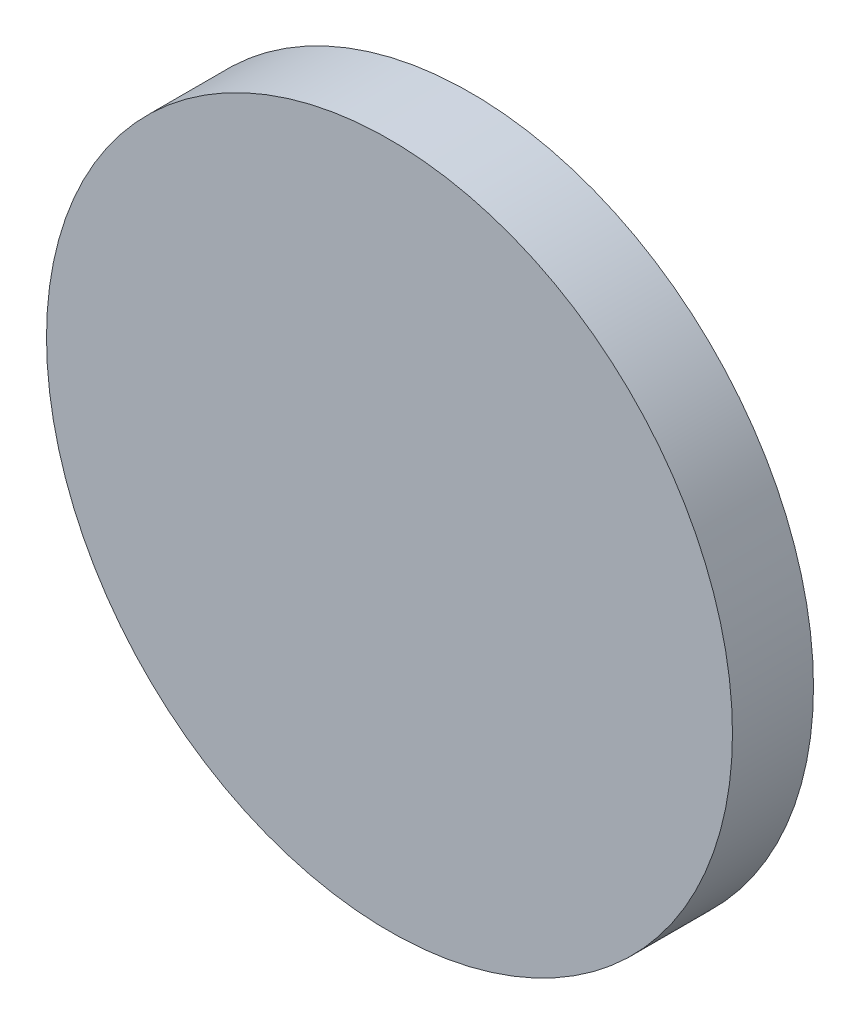
SolidWorks part; units mm, degrees
ref_plane "前视基准面" through (0, 0, 0) normal (0, 0, 1) x (1, 0, 0)
ref_plane "上视基准面" through (0, 0, 0) normal (0, 1, 0) x (1, 0, 0)
ref_plane "右视基准面" through (0, 0, 0) normal (1, 0, 0) x (0, 0, -1)
sketch "草图1" plane through (0, 0, 0) normal (0, 0, 1) x (1, 0, 0)
  circle A0 centre (0, 0) radius 12.7
  dimension "D1" = 25.4
extrude "凸台-拉伸1" add sketch "草图1" along normal blind 3 contours A0
